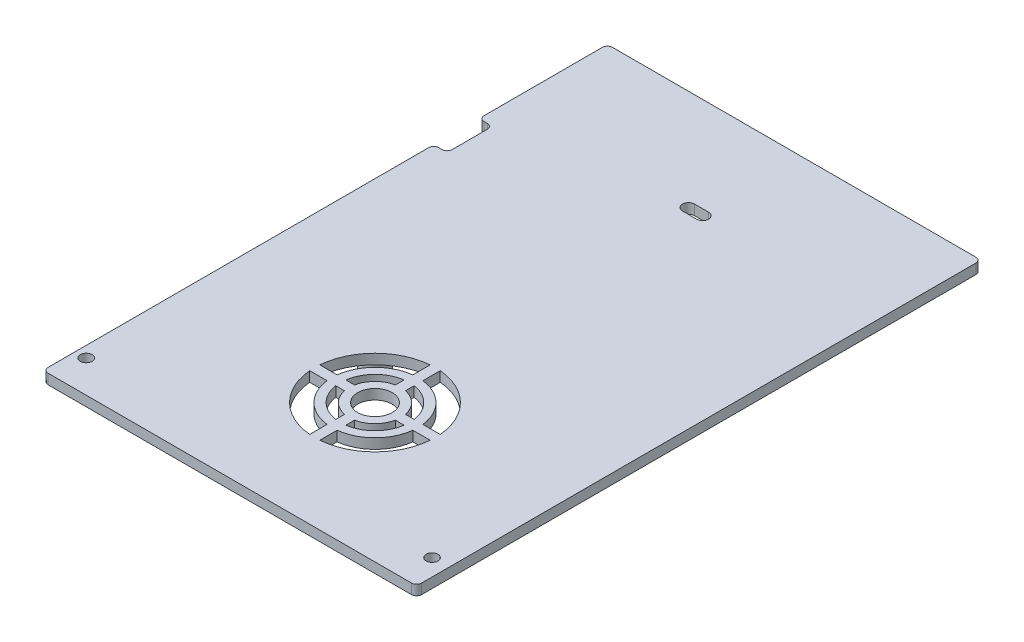
SolidWorks part; units mm, degrees
ref_plane "Plano frontal" through (0, 0, 0) normal (0, 0, 1) x (1, 0, 0)
ref_plane "Plano superior" through (0, 0, 0) normal (0, 1, 0) x (1, 0, 0)
ref_plane "Plano direito" through (0, 0, 0) normal (1, 0, 0) x (0, 0, -1)
sketch "Esboço1" plane through (0, 0, 0) normal (0, 1, 0) x (1, 0, 0)
  line L0 (-55.63, 45.795) -> (-55.63, 84.055)
  line L1 (-55.63, -84.055) -> (55.63, -84.055)
  line L2 (-55.63, -84.055) -> (-55.63, 32.315)
  line L3 (-55.63, 84.055) -> (55.63, 84.055)
  line L4 (55.63, -84.055) -> (55.63, 84.055)
  line L5 (0, 0) -> (55.63, 84.055) construction
  line L6 (-55.63, 84.055) -> (0, 0) construction
  line L7 (-55.63, 32.315) -> (-51.63, 32.315)
  line L9 (-55.63, 45.795) -> (-51.63, 45.795)
  line L10 (-51.63, 32.315) -> (-51.63, 45.795)
  line L11 (0.63, -53.1251) -> (0.63, -50.5118)
  line L17 (0.63, -60.8824) -> (0.63, -55.7172)
  line L23 (3.63, -60.8824) -> (3.63, -55.7172)
  line L27 (3.63, -53.1251) -> (3.63, -50.5118)
  line L29 (14.9022, -41.445) -> (20.0674, -41.445)
  line L33 (-15.8074, -44.445) -> (-10.6422, -44.445)
  line L37 (-15.8074, -41.445) -> (-10.6422, -41.445)
  line L41 (3.63, -30.1728) -> (3.63, -25.0076)
  line L44 (0.63, -30.1728) -> (0.63, -25.0076)
  line L45 (-8.0501, -41.445) -> (-5.4368, -41.445)
  line L48 (-8.0501, -44.445) -> (-5.4368, -44.445)
  line L49 (14.9022, -44.445) -> (20.0674, -44.445)
  line L51 (0.63, -35.3782) -> (0.63, -32.7649)
  line L53 (3.63, -35.3782) -> (3.63, -32.7649)
  line L54 (9.6968, -41.445) -> (12.3101, -41.445)
  line L55 (9.6968, -44.445) -> (12.3101, -44.445)
  circle A17 centre (2.13, -42.945) radius 5.145
  arc A18 (0.63, -35.3782) -> (-5.4368, -41.445) centre (2.13, -42.945) ccw
  arc A19 (0.63, -32.7649) -> (-8.0501, -41.445) centre (2.13, -42.945) ccw
  arc A20 (0.63, -30.1728) -> (-10.6422, -41.445) centre (2.13, -42.945) ccw
  arc A21 (0.63, -25.0076) -> (-15.8074, -41.445) centre (2.13, -42.945) ccw
  arc A22 (20.0674, -41.445) -> (3.63, -25.0076) centre (2.13, -42.945) ccw
  arc A23 (14.9022, -41.445) -> (3.63, -30.1728) centre (2.13, -42.945) ccw
  arc A24 (12.3101, -41.445) -> (3.63, -32.7649) centre (2.13, -42.945) ccw
  arc A25 (9.6968, -41.445) -> (3.63, -35.3782) centre (2.13, -42.945) ccw
  arc A26 (-15.8074, -44.445) -> (0.63, -60.8824) centre (2.13, -42.945) ccw
  arc A27 (-10.6422, -44.445) -> (0.63, -55.7172) centre (2.13, -42.945) ccw
  arc A28 (-8.0501, -44.445) -> (0.63, -53.1251) centre (2.13, -42.945) ccw
  arc A29 (-5.4368, -44.445) -> (0.63, -50.5118) centre (2.13, -42.945) ccw
  arc A30 (3.63, -60.8824) -> (20.0674, -44.445) centre (2.13, -42.945) ccw
  arc A31 (3.63, -55.7172) -> (14.9022, -44.445) centre (2.13, -42.945) ccw
  arc A32 (3.63, -53.1251) -> (12.3101, -44.445) centre (2.13, -42.945) ccw
  arc A33 (3.63, -50.5118) -> (9.6968, -44.445) centre (2.13, -42.945) ccw
  point P0 (0, 0)
  dimension "D6" = 10.29
  dimension "D7" = 41.11
  dimension "D8" = 57.76
  dimension "D9" = 15.428
  dimension "D10" = 20.58
  dimension "D11" = 25.72
  dimension "D12" = 36
  dimension "D1" = 111.26
  dimension "D2" = 168.11
  dimension "D3" = 13.48
  dimension "D4" = 4
  dimension "D5" = 38.26
extrude "Ressalto-extrusão1" add sketch "Esboço1" along normal blind 3
sketch "Esboço2" plane through (0, 3, 0) normal (0, 1, 0) x (1, 0, 0)
  line L0 (-55.63, -84.055) -> (-55.63, 32.315) construction
  line L1 (-55.63, -84.055) -> (55.63, -84.055) construction
  line L2 (55.63, -84.055) -> (55.63, 84.055) construction
  line L3 (-1.47, 54.055) -> (2.73, 54.055) construction
  line L4 (-1.47, 55.855) -> (2.73, 55.855)
  line L5 (-1.47, 52.255) -> (2.73, 52.255)
  line L6 (-55.63, 84.055) -> (55.63, 84.055) construction
  line L7 (-55.63, 45.795) -> (-55.63, 84.055) construction
  circle A0 centre (-52.37, -74.445) radius 1.75
  circle A1 centre (50.63, -74.445) radius 1.75
  arc A2 (-1.47, 55.855) -> (-1.47, 52.255) centre (-1.47, 54.055) ccw
  arc A3 (2.73, 52.255) -> (2.73, 55.855) centre (2.73, 54.055) ccw
  point P12 (0.63, 54.055)
  dimension "D1" = 3.26
  dimension "D2" = 9.61
  dimension "D3" = 3.5
  dimension "D4" = 9.61
  dimension "D5" = 5
  dimension "D6" = 1.8
  dimension "D9" = 54.16
  dimension "D7" = 4.2
  dimension "D8" = 28.2
extrude "Corte-extrusão1" cut sketch "Esboço2" against normal through all
fillet "Filete1" radius 1.5 8 edges at (-51.63, 1.5, -32.315) (-55.63, 1.5, -32.315) (-51.63, 1.5, -45.795) (-55.63, 1.5, -45.795) (-55.63, 1.5, -84.055) (55.63, 1.5, -84.055) (55.63, 1.5, 84.055) (-55.63, 1.5, 84.055)
sketch "Esboço3" plane through (0, 0, 0) normal (0, -1, 0) x (1, 0, 0)
  line L0 (2.13, 42.945) -> (2.13, 16.7229) construction
  line L1 (2.13, 42.945) -> (44.4951, 42.945) construction
  circle A0 centre (18.13, 26.945) radius 3.7
  circle A2 centre (2.13, 42.945) radius 5.145 construction
  circle A3 centre (18.13, 58.945) radius 3.7
  circle A4 centre (-13.87, 58.945) radius 3.7
  circle A5 centre (-13.87, 26.945) radius 3.7
  dimension "D1" = 16
  dimension "D2" = 16
  dimension "D5" = 7.4
extrude "Ressalto-extrusão2" add sketch "Esboço3" along normal blind 4.2
sketch "Esboço4" plane through (0, -4.2, 0) normal (0, -1, 0) x (1, 0, 0)
  line L0 (2.13, 42.945) -> (2.13, 71.7233) construction
  line L1 (2.13, 42.945) -> (-31.3506, 42.945) construction
  circle A0 centre (-13.87, 58.945) radius 2.2
  circle A1 centre (18.13, 58.945) radius 2.2
  circle A2 centre (18.13, 26.945) radius 2.2
  circle A3 centre (-13.87, 26.945) radius 2.2
  dimension "D1" = 4.4
extrude "Corte-extrusão2" cut sketch "Esboço4" against normal blind 4.2
